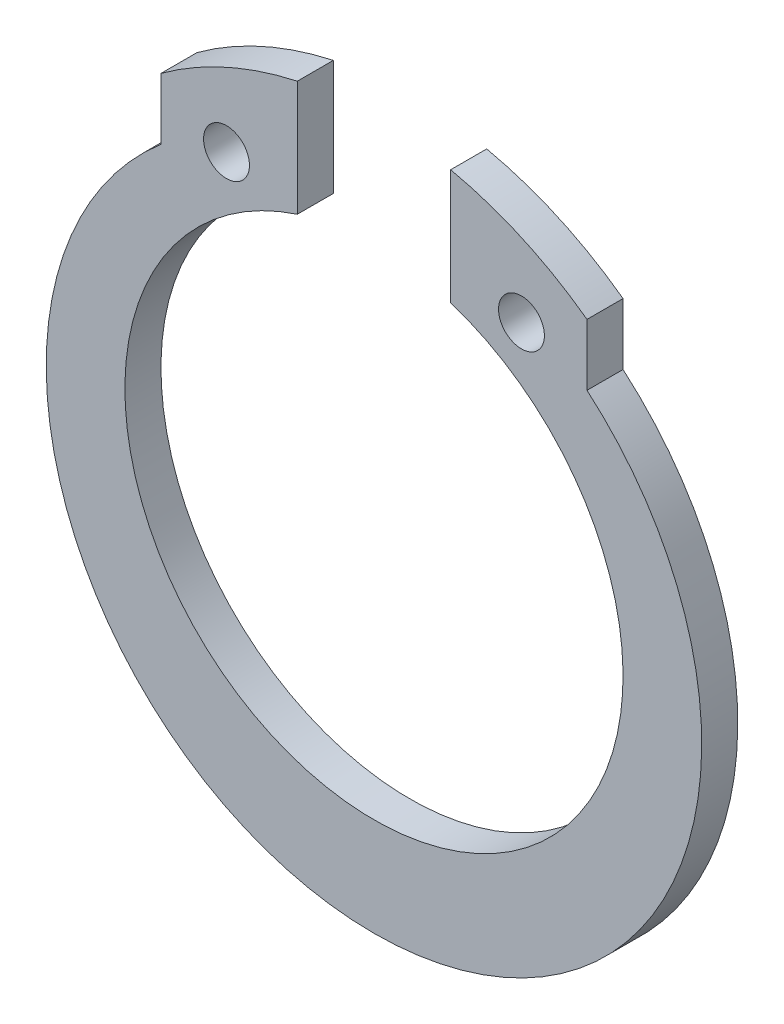
SolidWorks part; units mm, degrees
ref_plane "Front Plane" through (0, 0, 0) normal (0, 0, 1) x (1, 0, 0)
ref_plane "Top Plane" through (0, 0, 0) normal (0, 1, 0) x (1, 0, 0)
ref_plane "Right Plane" through (0, 0, 0) normal (1, 0, 0) x (0, 0, -1)
sketch "Sketch1" plane through (0, 0, 0) normal (0, 0, 1) x (1, 0, 0)
  line L0 (-3.25, 4.7371) -> (-3.25, 3.7997)
  line L1 (0, 0) -> (0, 5.3312) construction
  line L2 (3.25, 4.7371) -> (3.25, 3.7997)
  arc A0 (-3.25, 3.7997) -> (3.25, 3.7997) centre (0, 0) ccw
  arc A1 (3.25, 4.7371) -> (-3.25, 4.7371) centre (0, 0.3) ccw
  dimension "D1" = 10
  dimension "D2" = 0.3
  dimension "D4" = 5.5
  dimension "D3" = 6.5
extrude "Boss-Extrude1" add sketch "Sketch1" against normal blind 0.55 contours A1 L0 A0 L2
sketch "Sketch2" plane through (0, 0, 0) normal (0, 0, 1) x (1, 0, 0)
  circle A0 centre (0, 0.3) radius 3.8
  arc A1 (3.25, 4.7371) -> (-3.25, 4.7371) centre (0, 0.3) ccw construction
  dimension "D1" = 7.6
extrude "Cut-Extrude1" cut sketch "Sketch2" against normal through all
sketch "Sketch3" plane through (0, 0, 0) normal (0, 0, 1) x (1, 0, 0)
  line L0 (0, 0) -> (0, 5.8) construction
  line L3 (-1.17, 5.6741) -> (-1.17, 3.9154)
  line L5 (1.17, 5.6741) -> (1.17, 3.9154)
  arc A0 (3.25, 4.7371) -> (-3.25, 4.7371) centre (0, 0.3) ccw construction
  arc A1 (1.17, 5.6741) -> (-1.17, 5.6741) centre (0, 0.3) ccw
  circle A2 centre (0, 0.3) radius 3.8 construction
  arc A3 (1.17, 3.9154) -> (-1.17, 3.9154) centre (0, 0.3) ccw
  dimension "D1" = 2.34
extrude "Cut-Extrude2" cut sketch "Sketch3" against normal through all
hole_wizard "Ø0.7 (0.7) Diameter Hole1" positions "Sketch5" profile "Sketch4" hole size "Ø0.7" standard "DIN" end condition up to next
sketch "Sketch5" plane through (0, 0, 0) normal (0, 0, 1) x (1, 0, 0)
  line L0 (0, 0) -> (0, 4.3775) construction
  circle A0 centre (0, 0.3) radius 4.5 construction
  arc A1 (-1.17, 3.9154) -> (1.17, 3.9154) centre (0, 0.3) ccw construction
  point P6 (-2.25, 4.1971)
  point P8 (2.25, 4.1971)
  dimension "D1" = 9
  dimension "D2" = 4.5
sketch "Sketch4" plane through (-2.25, 4.1971, 0) normal (1, 0, 0) x (0, -1, 0)
  line L0 (0, 0) -> (0, 0.55)
  line L1 (0, 0.55) -> (0.35, 0.55)
  line L2 (0.35, 0.55) -> (0.35, 0)
  line L5 (0.35, 0) -> (0, 0)
  line L11 (0, -6.35) -> (0, 107.95) construction
  dimension "Thru Hole Dia." = 0.7
  dimension "Thru Hole Depth" = 0.55
